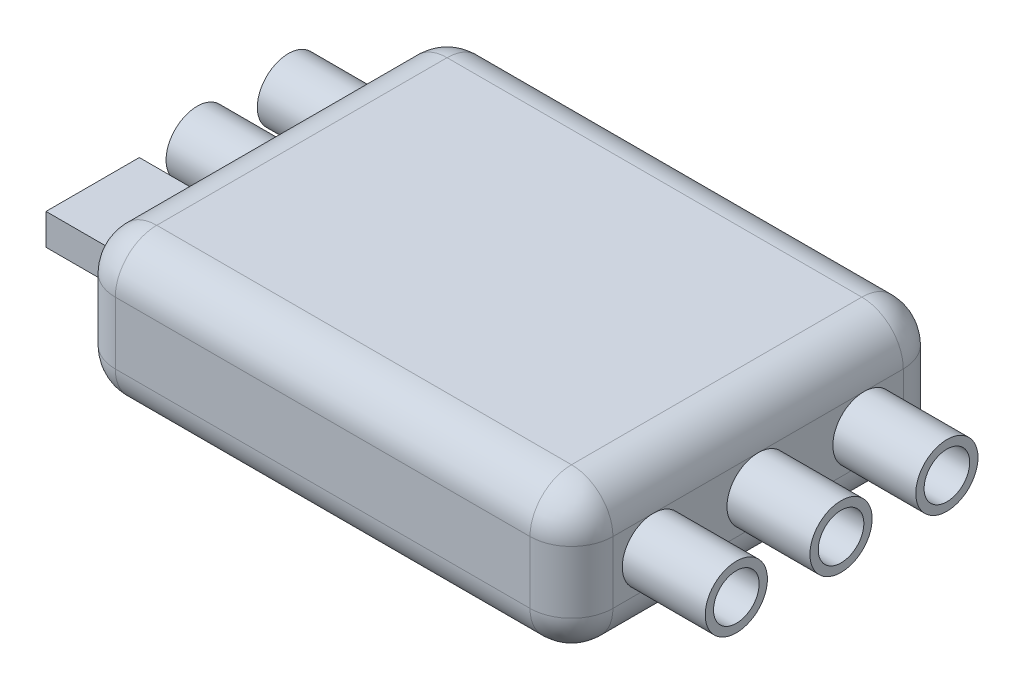
SolidWorks part; units mm, degrees
ref_plane "Front Plane" through (0, 0, 0) normal (0, 0, 1) x (1, 0, 0)
ref_plane "Top Plane" through (0, 0, 0) normal (0, 1, 0) x (1, 0, 0)
ref_plane "Right Plane" through (0, 0, 0) normal (1, 0, 0) x (0, 0, -1)
sketch "Sketch2" plane through (0, 0, 0) normal (0, 1, 0) x (1, 0, 0)
  line L1 (-10, 9) -> (10, 9)
  line L2 (-12, 7) -> (-12, -7)
  line L3 (-10, -9) -> (10, -9)
  line L4 (12, 7) -> (12, -7)
  line L5 (-12, 9) -> (12, -9) construction
  line L6 (-12, -9) -> (12, 9) construction
  arc A0 (10, 9) -> (12, 7) centre (10, 7) cw
  arc A1 (-12, -7) -> (-10, -9) centre (-10, -7) ccw
  arc A2 (-10, 9) -> (-12, 7) centre (-10, 7) ccw
  arc A3 (10, -9) -> (12, -7) centre (10, -7) ccw
  point P0 (0, 0)
  dimension "D3" = 2
  dimension "D1" = 24
  dimension "D2" = 18
extrude "Boss-Extrude1" add sketch "Sketch2" along normal blind 7
fillet "Fillet1" radius 2 16 edges at (0, 0, -9) (-11.4142, 0, -8.4142) (-12, 0, 0) (-11.4142, 0, 8.4142) (0, 0, 9) (11.4142, 0, 8.4142) (12, 0, 0) (11.4142, 0, -8.4142) (12, 7, 0) (11.4142, 7, 8.4142) (0, 7, 9) (-11.4142, 7, 8.4142) (-12, 7, 0) (-11.4142, 7, -8.4142) (0, 7, -9) (11.4142, 7, -8.4142)
sketch "Sketch3" plane through (12, 0, 0) normal (1, 0, 0) x (0, 0, -1)
  line L0 (-7, 3.5) -> (7, 3.5) construction
  line L1 (-7, 5) -> (-7, 2) construction
  line L2 (7, 5) -> (7, 2) construction
  circle A0 centre (-5.0497, 3.5) radius 1.5
  circle A1 centre (-5.0497, 3.5) radius 1.1
  circle A2 centre (0, 3.5) radius 1.5
  circle A3 centre (0, 3.5) radius 1.1
  circle A4 centre (5.1047, 3.5) radius 1.5
  circle A5 centre (5.1047, 3.5) radius 1.1
  dimension "D1" = 3
  dimension "D2" = 0.4
extrude "Boss-Extrude2" add sketch "Sketch3" along normal blind 4
sketch "Sketch4" plane through (-12, 0, 0) normal (-1, 0, 0) x (0, 0, 1)
  line L0 (-7, 3.5) -> (7, 3.5) construction
  line L1 (-7, 5) -> (-7, 2) construction
  line L2 (7, 5) -> (7, 2) construction
  line L4 (6.3407, 4.25) -> (1.8407, 4.25)
  line L5 (6.3407, 4.25) -> (6.3407, 2.75)
  line L6 (6.3407, 2.75) -> (1.8407, 2.75)
  line L7 (1.8407, 4.25) -> (1.8407, 2.75)
  circle A0 centre (-5.3494, 3.5) radius 1.5
  circle A1 centre (-5.3494, 3.5) radius 1.1
  circle A2 centre (-0.9494, 3.5) radius 1.5
  circle A3 centre (-0.9494, 3.5) radius 1.1
  dimension "D3" = 3
  dimension "D4" = 0.4
  dimension "D1" = 4.5
  dimension "D2" = 1.5
  dimension "D5" = 4.4
extrude "Boss-Extrude3" add sketch "Sketch4" along normal blind 4
